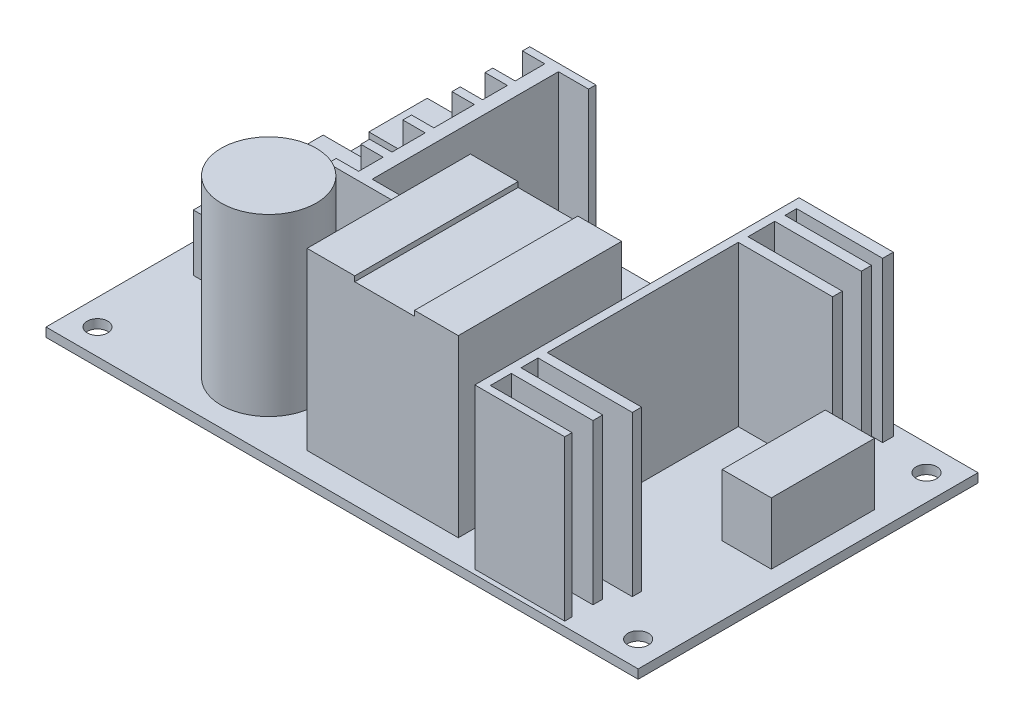
SolidWorks part; units mm, degrees
ref_plane "Front Plane" through (0, 0, 0) normal (0, 0, 1) x (1, 0, 0)
ref_plane "Top Plane" through (0, 0, 0) normal (0, 1, 0) x (1, 0, 0)
ref_plane "Right Plane" through (0, 0, 0) normal (1, 0, 0) x (0, 0, -1)
sketch "Sketch1" plane through (0, 0, 0) normal (0, 1, 0) x (1, 0, 0)
  line L1 (-44.3728, 25.8442) -> (70.6272, 25.8442)
  line L2 (-44.3728, 25.8442) -> (-44.3728, -40.1558)
  line L3 (-44.3728, -40.1558) -> (70.6272, -40.1558)
  line L4 (70.6272, 25.8442) -> (70.6272, -40.1558)
  dimension "D1" = 115
  dimension "D2" = 66
extrude "Boss-Extrude1" add sketch "Sketch1" along normal blind 1.75
sketch "Sketch2" plane through (0, 1.75, 0) normal (0, 1, 0) x (1, 0, 0)
  line L0 (70.6272, 25.8442) -> (-44.3728, 25.8442) construction
  line L1 (-44.3728, 25.8442) -> (-44.3728, -40.1558) construction
  line L2 (-44.3728, -40.1558) -> (70.6272, -40.1558) construction
  line L3 (13.1272, 42.2033) -> (13.1272, -51.4084)
  line L4 (70.6272, -40.1558) -> (70.6272, 25.8442) construction
  circle A0 centre (-39.3728, 20.8442) radius 2
  circle A1 centre (-39.3728, -35.1558) radius 2
  circle A2 centre (65.6272, -35.1558) radius 2
  circle A3 centre (65.6272, 20.8442) radius 2
  dimension "D1" = 4
  dimension "D2" = 4
  dimension "D3" = 5
  dimension "D4" = 5
  dimension "D5" = 5
  dimension "D6" = 5
  dimension "D7" = 57.5
extrude "Cut-Extrude1" cut sketch "Sketch2" against normal blind 1.75 contours A3 | A2 | A0 | A1
sketch "Sketch3" plane through (0, 1.75, 0) normal (0, 1, 0) x (1, 0, 0)
  line L1 (-33.8387, 23.3367) -> (-16.5628, 23.3367)
  line L2 (-33.8387, 23.3367) -> (-33.8387, 12.0082)
  line L3 (-33.8387, 12.0082) -> (-16.5628, 12.0082)
  line L4 (-16.5628, 23.3367) -> (-16.5628, 12.0082)
extrude "Boss-Extrude2" add sketch "Sketch3" along normal blind 12
sketch "Sketch4" plane through (0, 1.75, 0) normal (0, 1, 0) x (1, 0, 0)
  line L1 (1.7516, -3.8516) -> (31.1112, -3.8516)
  line L2 (1.7516, -3.8516) -> (1.7516, -35.5713)
  line L3 (1.7516, -35.5713) -> (31.1112, -35.5713)
  line L4 (31.1112, -3.8516) -> (31.1112, -35.5713)
extrude "Boss-Extrude3" add sketch "Sketch4" along normal blind 34 contours L2 L1 L4 L3
sketch "Sketch5" plane through (0, 1.75, 0) normal (0, 1, 0) x (1, 0, 0)
  circle A0 centre (-14.2027, -27.075) radius 9.2328
extrude "Boss-Extrude4" add sketch "Sketch5" along normal blind 34
sketch "Sketch6" plane through (0, 1.75, 0) normal (0, 1, 0) x (1, 0, 0)
  line L1 (57.261, 9.5537) -> (66.7958, 9.5537)
  line L2 (57.261, 9.5537) -> (57.261, -10.4599)
  line L3 (57.261, -10.4599) -> (66.7958, -10.4599)
  line L4 (66.7958, 9.5537) -> (66.7958, -10.4599)
extrude "Boss-Extrude5" add sketch "Sketch6" along normal blind 12 contours L2 L1 L4 L3
sketch "Sketch7" plane through (0, 1.75, 0) normal (0, 1, 0) x (1, 0, 0)
  line L1 (38.0027, 23.7143) -> (39.6075, 23.7143)
  line L2 (38.0027, 23.7143) -> (38.0027, -39.2531)
  line L3 (38.0027, -39.2531) -> (39.6075, -39.2531)
  line L4 (39.6075, 23.7143) -> (39.6075, -39.2531)
  line L5 (39.6075, 23.7143) -> (56.317, 23.7143)
  line L6 (39.6075, 23.7143) -> (39.6075, 21.6374)
  line L7 (39.6075, 21.6374) -> (56.317, 21.6374)
  line L8 (56.317, 23.7143) -> (56.317, 21.6374)
  line L9 (39.6075, 19.3717) -> (56.4114, 19.3717)
  line L10 (39.6075, 19.3717) -> (39.6075, 17.3892)
  line L11 (39.6075, 17.3892) -> (56.4114, 17.3892)
  line L12 (56.4114, 19.3717) -> (56.4114, 17.3892)
  line L13 (39.6075, 12.197) -> (57.9219, 12.197)
  line L14 (39.6075, 12.197) -> (39.6075, 10.309)
  line L15 (39.6075, 10.309) -> (57.9219, 10.309)
  line L16 (57.9219, 12.197) -> (57.9219, 10.309)
  line L17 (39.6075, -26.7918) -> (57.9219, -26.7918)
  line L18 (39.6075, -26.7918) -> (39.6075, -28.5855)
  line L19 (39.6075, -28.5855) -> (57.9219, -28.5855)
  line L20 (57.9219, -26.7918) -> (57.9219, -28.5855)
  line L21 (39.6075, -31.8896) -> (55.4674, -31.8896)
  line L22 (39.6075, -31.8896) -> (39.6075, -33.7777)
  line L23 (39.6075, -33.7777) -> (55.4674, -33.7777)
  line L24 (55.4674, -31.8896) -> (55.4674, -33.7777)
  line L25 (39.6075, -39.2531) -> (55.4674, -39.2531)
  line L26 (39.6075, -39.2531) -> (39.6075, -37.837)
  line L27 (39.6075, -37.837) -> (55.4674, -37.837)
  line L28 (55.4674, -39.2531) -> (55.4674, -37.837)
extrude "Boss-Extrude6" add sketch "Sketch7" along normal blind 31 contours L20 L17 L4 L19 | L4 L1 L2 L3 | L24 L21 L4 L23 | L25 L28 L27 L4 | L16 L13 L4 L15 | L8 L5 L4 L7 | L12 L9 L4 L11
sketch "Sketch8" plane through (0, 1.75, 0) normal (0, 1, 0) x (1, 0, 0)
  line L1 (-9.197, 21.543) -> (-6.556, 21.543)
  line L2 (-9.197, 21.543) -> (-9.197, -16.2185)
  line L3 (-9.197, -16.2185) -> (-6.556, -16.2185)
  line L4 (-6.556, 21.543) -> (-6.556, -16.2185)
  line L5 (-13.5419, 22.9591) -> (-0.7029, 22.9591)
  line L6 (-13.5419, 22.9591) -> (-13.5419, 21.543)
  line L7 (-13.5419, 21.543) -> (-0.7029, 21.543)
  line L8 (-0.7029, 22.9591) -> (-0.7029, 21.543)
  line L9 (-13.5419, -14.6137) -> (-0.7029, -14.6137)
  line L10 (-13.5419, -14.6137) -> (-13.5419, -16.2185)
  line L11 (-13.5419, -16.2185) -> (-0.7029, -16.2185)
  line L12 (-0.7029, -14.6137) -> (-0.7029, -16.2185)
  line L13 (-13.5419, 15.7844) -> (-9.197, 15.7844)
  line L14 (-13.5419, 15.7844) -> (-13.5419, 14.2739)
  line L15 (-13.5419, 14.2739) -> (-9.197, 14.2739)
  line L16 (-9.197, 15.7844) -> (-9.197, 14.2739)
  line L17 (-13.5419, 9.4593) -> (-9.197, 9.4593)
  line L18 (-13.5419, 9.4593) -> (-13.5419, 7.8545)
  line L19 (-13.5419, 7.8545) -> (-9.197, 7.8545)
  line L20 (-9.197, 9.4593) -> (-9.197, 7.8545)
  line L21 (-13.5419, 0) -> (-9.197, 0)
  line L22 (-13.5419, 0) -> (-13.5419, -1.6803)
  line L23 (-13.5419, -1.6803) -> (-9.197, -1.6803)
  line L24 (-9.197, 0) -> (-9.197, -1.6803)
  line L25 (-13.5396, -8.1505) -> (-9.197, -8.1505)
  line L26 (-13.5396, -8.1505) -> (-13.5396, -9.8497)
  line L27 (-13.5396, -9.8497) -> (-9.197, -9.8497)
  line L28 (-9.197, -8.1505) -> (-9.197, -9.8497)
extrude "Boss-Extrude7" add sketch "Sketch8" along normal blind 31 contours L26 L27 L2 L25 | L2 L9 L4 L1 | L21 L24 L23 L22 | L17 L20 L19 L18 | L15 L16 L13 L14 | L5 L8 L7 L6
sketch "Sketch9" plane through (0, 35.75, 0) normal (0, 1, 0) x (1, 0, 0)
  line L0 (1.7516, -3.8516) -> (31.1112, -3.8516) construction
  line L1 (11.0031, -3.8516) -> (22.6148, -3.8516)
  line L2 (11.0031, -3.8516) -> (11.0031, -35.5713)
  line L3 (11.0031, -35.5713) -> (22.6148, -35.5713)
  line L4 (22.6148, -3.8516) -> (22.6148, -35.5713)
  line L5 (1.7516, -35.5713) -> (31.1112, -35.5713) construction
extrude "Cut-Extrude2" cut sketch "Sketch9" against normal blind 1
sketch "Sketch11" plane through (0, 1.75, 0) normal (0, 1, 0) x (1, 0, 0)
  line L1 (-38.7477, 8.0433) -> (-20.2445, 8.0433)
  line L2 (-38.7477, 8.0433) -> (-38.7477, 2.9454)
  line L3 (-38.7477, 2.9454) -> (-20.2445, 2.9454)
  line L4 (-20.2445, 8.0433) -> (-20.2445, 2.9454)
  line L5 (-38.7477, -12.348) -> (-20.2445, -12.348)
  line L6 (-38.7477, -12.348) -> (-38.7477, -17.1626)
  line L7 (-38.7477, -17.1626) -> (-20.2445, -17.1626)
  line L8 (-20.2445, -12.348) -> (-20.2445, -17.1626)
extrude "Boss-Extrude8" add sketch "Sketch11" along normal blind 11
